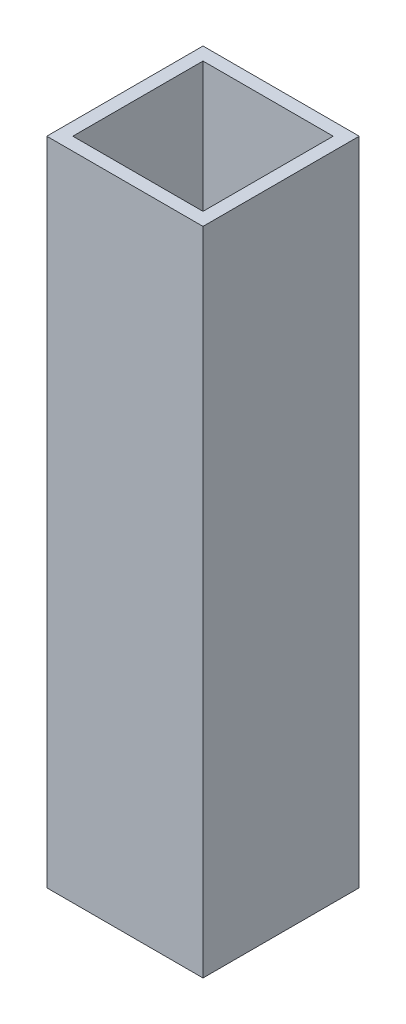
SolidWorks part; units mm, degrees
material "Custom Plastic"
ref_plane "Front Plane" through (0, 0, 0) normal (0, 0, 1) x (1, 0, 0)
ref_plane "Top Plane" through (0, 0, 0) normal (0, 1, 0) x (1, 0, 0)
ref_plane "Right Plane" through (0, 0, 0) normal (1, 0, 0) x (0, 0, -1)
sketch "Sketch1" plane through (0, 0, 0) normal (0, 0, 1) x (1, 0, 0)
  line L1 (-31.7391, 49.7826) -> (-7.7391, 49.7826)
  line L2 (-31.7391, 49.7826) -> (-31.7391, -50.2174)
  line L3 (-31.7391, -50.2174) -> (-7.7391, -50.2174)
  line L4 (-7.7391, 49.7826) -> (-7.7391, -50.2174)
  dimension "D1" = 24
  dimension "D2" = 100
extrude "Boss-Extrude1" add sketch "Sketch1" against normal blind 24
sketch "Sketch2" plane through (0, 49.7826, 0) normal (0, 1, 0) x (1, 0, 0)
  line L8 (-29.7391, 2) -> (-9.7391, 2)
  line L9 (-9.7391, 2) -> (-9.7391, 22)
  line L10 (-9.7391, 22) -> (-29.7391, 22)
  line L11 (-29.7391, 22) -> (-29.7391, 2)
  line L12 (-29.7391, 2) -> (-9.7391, 2)
  line L13 (-9.7391, 2) -> (-9.7391, 22)
  line L14 (-9.7391, 22) -> (-29.7391, 22)
  line L15 (-29.7391, 22) -> (-29.7391, 2)
  dimension "D1" = 2
extrude "Cut-Extrude1" cut sketch "Sketch2" against normal blind 200
